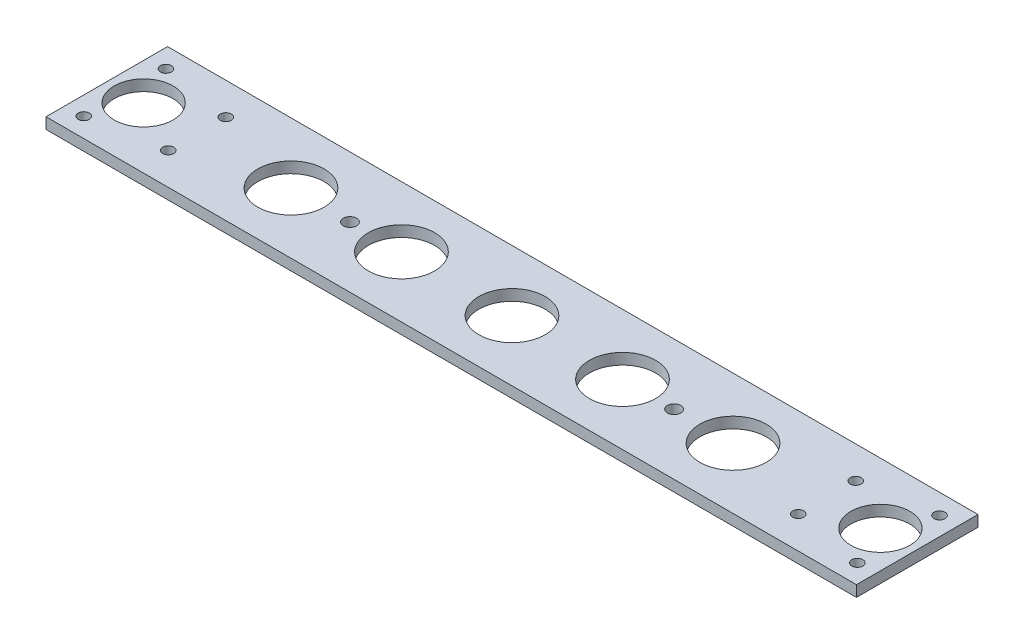
SolidWorks part; units mm, degrees
ref_plane "前视基准面" through (0, 0, 0) normal (0, 0, 1) x (1, 0, 0)
ref_plane "上视基准面" through (0, 0, 0) normal (0, 1, 0) x (1, 0, 0)
ref_plane "右视基准面" through (0, 0, 0) normal (1, 0, 0) x (0, 0, -1)
sketch "草图1" plane through (0, 0, 0) normal (0, 1, 0) x (1, 0, 0)
  line L0 (110, -16.5) -> (154, -16.5) construction
  line L1 (0, 0) -> (220, 0)
  line L2 (0, 0) -> (0, -33)
  line L3 (0, -33) -> (220, -33)
  line L4 (220, 0) -> (220, -33)
  line L5 (110, -16.5) -> (66, -16.5) construction
  circle A0 centre (5, -27.75) radius 1.5
  circle A1 centre (5, -5.45) radius 1.5
  circle A2 centre (24.5, -8.7) radius 1.5
  circle A3 centre (24.5, -24.3) radius 1.5
  circle A4 centre (195.5, -8.7) radius 1.5
  circle A5 centre (195.5, -24.3) radius 1.5
  circle A6 centre (215, -27.75) radius 1.5
  circle A7 centre (215, -5.45) radius 1.5
  circle A8 centre (110, -16.5) radius 9
  circle A9 centre (140, -16.5) radius 9
  circle A10 centre (10, -16.5) radius 8
  circle A11 centre (210, -16.5) radius 8
  circle A12 centre (170, -16.5) radius 9
  circle A13 centre (80, -16.5) radius 9
  circle A14 centre (50, -16.5) radius 9
  circle A15 centre (154, -16.5) radius 1.8
  circle A16 centre (66, -16.5) radius 1.8
extrude "凸台-拉伸1" add sketch "草图1" along normal blind 3
